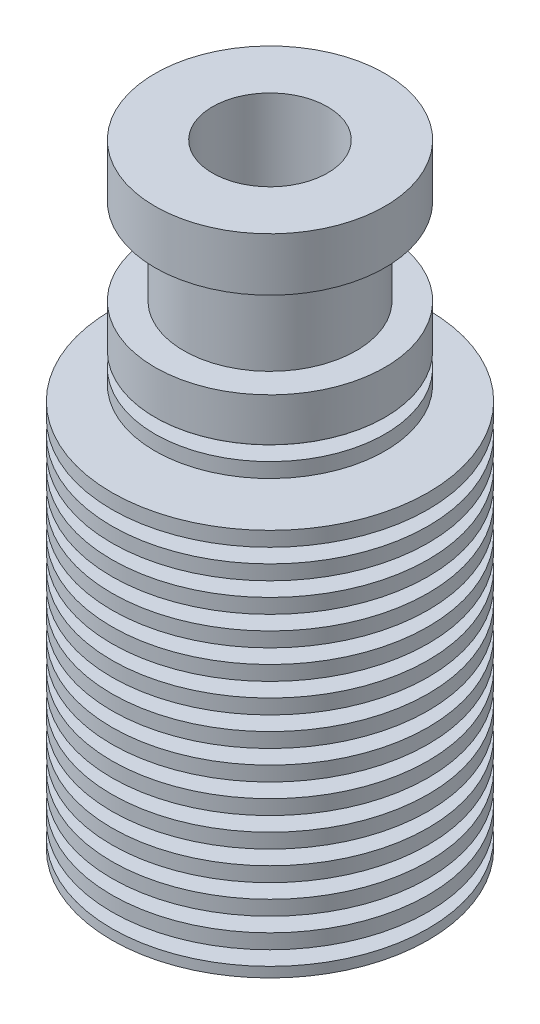
SolidWorks part; units mm, degrees
material "3.0205 (EN-AW 1200)"
ref_plane "Alzado" through (0, 0, 0) normal (0, 0, 1) x (1, 0, 0)
ref_plane "Planta" through (0, 0, 0) normal (0, 1, 0) x (1, 0, 0)
ref_plane "Vista lateral" through (0, 0, 0) normal (1, 0, 0) x (0, 0, -1)
sketch "Croquis1" plane through (0, 0, 0) normal (0, 0, 1) x (1, 0, 0)
  line L0 (0, 0) -> (0, 42.7) construction
  line L1 (0, 42.7) -> (8, 42.7)
  line L2 (8, 42.7) -> (8, 39)
  line L3 (8, 39) -> (6, 39)
  line L4 (6, 39) -> (6, 33)
  line L5 (6, 33) -> (8, 33)
  line L6 (8, 33) -> (8, 30)
  line L7 (8, 30) -> (11, 30)
  line L8 (11, 30) -> (11, 0)
  line L9 (11, 0) -> (0, 0)
  line L10 (0, 36.2) -> (4, 36.2)
  line L11 (4, 36.2) -> (4, 42.7)
  line L12 (4, 36.2) -> (2.1, 34.6057)
  line L13 (2.1, 34.6057) -> (0, 34.6057)
  line L14 (0, 15.1) -> (3, 15.1)
  line L15 (3, 15.1) -> (3, 0)
  line L16 (3, 15.1) -> (2.1, 15.4276)
  line L17 (2.1, 15.4276) -> (0, 15.4276)
  line L18 (2.1, 34.6057) -> (2.1, 15.4276)
  dimension "D1" = 3.7
  dimension "D2" = 8
  dimension "D3" = 6
  dimension "D4" = 3
  dimension "D5" = 42.7
  dimension "D6" = 6
  dimension "D7" = 11
  dimension "D8" = 4
  dimension "D9" = 6.5
  dimension "D10" = 40
  dimension "D11" = 2.1
  dimension "D12" = 3
  dimension "D13" = 15.1
  dimension "D14" = 2.1
  dimension "D15" = 20
revolve "Revolución2" add sketch "Croquis1" angle 360 about L0
sketch "Croquis2" plane through (0, 0, 0) normal (0, 0, 1) x (1, 0, 0)
  line L0 (11, 0.7) -> (3, 0.7)
  line L1 (11, 0) -> (11, 30) construction
  line L3 (3, 0) -> (3, 15.1) construction
  line L5 (3, 0.7) -> (3, 1.7)
  line L6 (3, 1.7) -> (11, 1.7)
  line L7 (11, 1.7) -> (11, 0.7)
  line L8 (-11, 0) -> (11, 0) construction
  line L9 (11, 2.72) -> (3, 2.72)
  line L10 (11, 3.72) -> (11, 2.72)
  line L11 (3, 3.72) -> (11, 3.72)
  line L12 (3, 2.72) -> (3, 3.72)
  line L13 (11, 4.74) -> (3, 4.74)
  line L14 (11, 5.74) -> (11, 4.74)
  line L15 (3, 5.74) -> (11, 5.74)
  line L16 (3, 4.74) -> (3, 5.74)
  line L17 (11, 6.76) -> (3, 6.76)
  line L18 (11, 7.76) -> (11, 6.76)
  line L19 (3, 7.76) -> (11, 7.76)
  line L20 (3, 6.76) -> (3, 7.76)
  line L21 (11, 8.78) -> (3, 8.78)
  line L22 (11, 9.78) -> (11, 8.78)
  line L23 (3, 9.78) -> (11, 9.78)
  line L24 (3, 8.78) -> (3, 9.78)
  line L25 (11, 10.8) -> (3, 10.8)
  line L26 (11, 11.8) -> (11, 10.8)
  line L27 (3, 11.8) -> (11, 11.8)
  line L28 (3, 10.8) -> (3, 11.8)
  line L29 (11, 12.82) -> (3, 12.82)
  line L30 (11, 13.82) -> (11, 12.82)
  line L31 (3, 13.82) -> (11, 13.82)
  line L32 (3, 12.82) -> (3, 13.82)
  line L33 (11, 14.84) -> (3, 14.84)
  line L34 (11, 15.84) -> (11, 14.84)
  line L35 (3, 15.84) -> (11, 15.84)
  line L36 (3, 14.84) -> (3, 15.84)
  line L37 (11, 16.86) -> (3, 16.86)
  line L38 (11, 17.86) -> (11, 16.86)
  line L39 (3, 17.86) -> (11, 17.86)
  line L40 (3, 16.86) -> (3, 17.86)
  line L41 (11, 18.88) -> (3, 18.88)
  line L42 (11, 19.88) -> (11, 18.88)
  line L43 (3, 19.88) -> (11, 19.88)
  line L44 (3, 18.88) -> (3, 19.88)
  line L45 (11, 20.9) -> (3, 20.9)
  line L46 (11, 21.9) -> (11, 20.9)
  line L47 (3, 21.9) -> (11, 21.9)
  line L48 (3, 20.9) -> (3, 21.9)
  line L49 (11, 22.92) -> (3, 22.92)
  line L50 (11, 23.92) -> (11, 22.92)
  line L51 (3, 23.92) -> (11, 23.92)
  line L52 (3, 22.92) -> (3, 23.92)
  line L53 (11, 24.94) -> (3, 24.94)
  line L54 (11, 25.94) -> (11, 24.94)
  line L55 (3, 25.94) -> (11, 25.94)
  line L56 (3, 24.94) -> (3, 25.94)
  line L57 (11, 26.96) -> (3, 26.96)
  line L58 (11, 27.96) -> (11, 26.96)
  line L59 (3, 27.96) -> (11, 27.96)
  line L60 (3, 26.96) -> (3, 27.96)
  line L61 (11, 28.98) -> (3, 28.98)
  line L62 (11, 29.98) -> (11, 28.98)
  line L63 (3, 29.98) -> (11, 29.98)
  line L64 (3, 28.98) -> (3, 29.98)
  line L65 (4, 0) -> (4, 29.98)
  line L66 (4, 29.98) -> (6.6229, 0)
  line L67 (4, 29.98) -> (4, 30)
  line L68 (8, 30) -> (-8, 30) construction
  line L69 (4, 30) -> (10.9932, 30)
  line L70 (11, 30) -> (-11, 30) construction
  line L71 (10.9932, 30) -> (11, 29.98)
  line L72 (0, 0) -> (0, 30) construction
  line L73 (8, 28.98) -> (8, 27.96)
  line L74 (11, 28.98) -> (11, 27.96)
  dimension "D1" = 0.7
  dimension "D2" = 1
  dimension "D4" = 4
  dimension "D5" = 5
  dimension "D6" = 8
  dimension "D3" = 15
revolve "Cortar-Revolución1" cut sketch "Croquis2" angle 360 about L72
sketch "Croquis3" plane through (0, 0, 0) normal (0, 0, 1) x (1, 0, 0)
  line L0 (10.9945, 30) -> (11.0943, 30)
  line L3 (11, 30) -> (-11, 30) construction
  line L4 (11.0943, 30) -> (11.0943, 29.98)
  line L5 (11.0943, 29.98) -> (7.9926, 29.98)
  line L6 (0, 0) -> (0, 29.98) construction
  line L7 (-3, 0) -> (3, 0) construction
  line L8 (-4, 29.98) -> (4, 29.98) construction
  line L9 (-11, 29.98) -> (11, 29.98) construction
  line L10 (7.9926, 29.98) -> (7.9926, 30)
  line L11 (8, 30) -> (-8, 30) construction
  line L12 (7.9926, 30) -> (10.9945, 30)
  line L13 (10.9945, 30) -> (10.9952, 30.0001)
revolve "Cortar-Revolución4" cut sketch "Croquis3" angle 360 about L6
